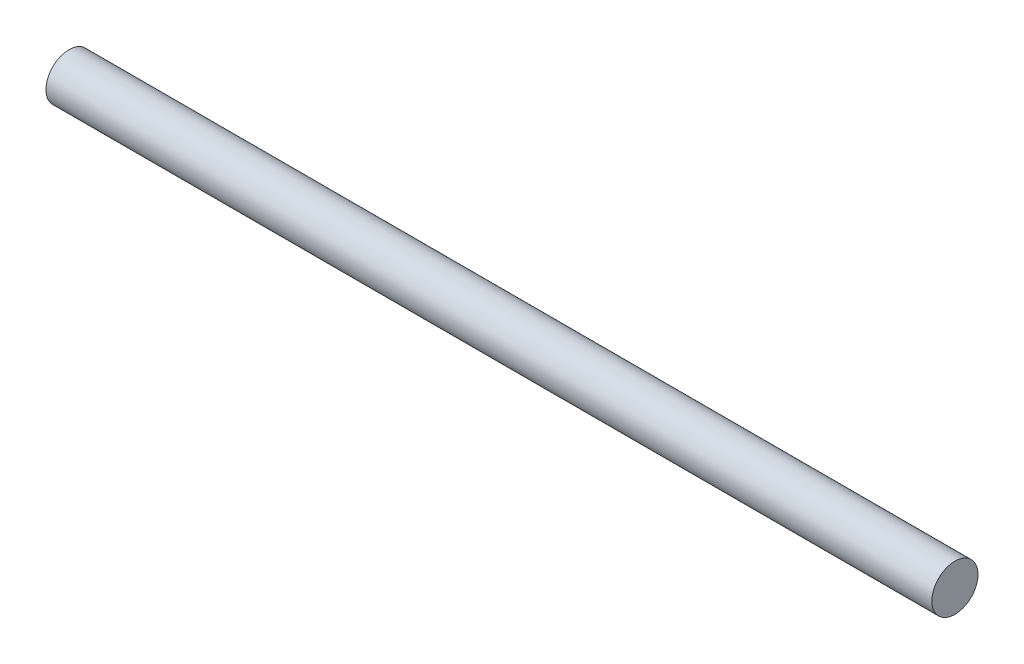
SolidWorks part; units mm, degrees
ref_plane "Front Plane" through (0, 0, 0) normal (0, 0, 1) x (1, 0, 0)
ref_plane "Top Plane" through (0, 0, 0) normal (0, 1, 0) x (1, 0, 0)
ref_plane "Right Plane" through (0, 0, 0) normal (1, 0, 0) x (0, 0, -1)
sketch "Sketch1" plane through (0, 0, 0) normal (1, 0, 0) x (0, 0, -1)
  circle A0 centre (0, 0) radius 2.5
  dimension "D1" = 5
extrude "Boss-Extrude1" add sketch "Sketch1" along normal blind 96
